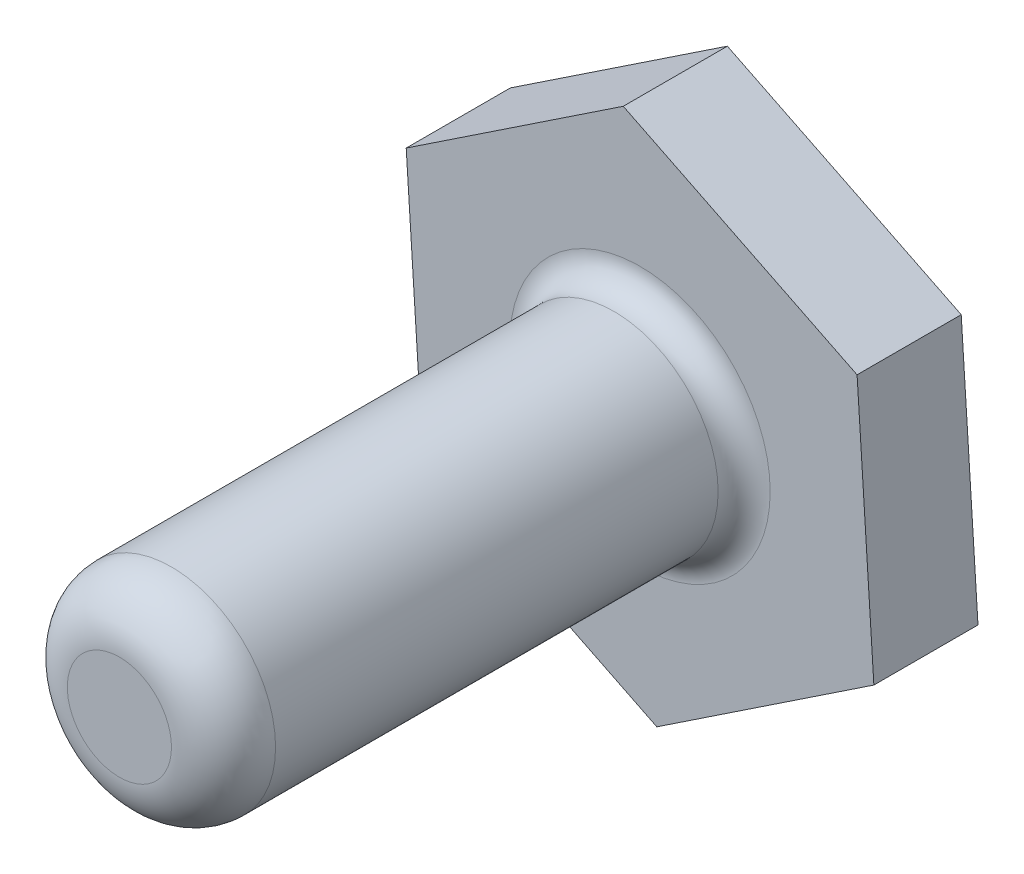
SolidWorks part; units mm, degrees
ref_plane "前视基准面" through (0, 0, 0) normal (0, 0, 1) x (1, 0, 0)
ref_plane "上视基准面" through (0, 0, 0) normal (0, 1, 0) x (1, 0, 0)
ref_plane "右视基准面" through (0, 0, 0) normal (1, 0, 0) x (0, 0, -1)
sketch "草图1" plane through (0, 0, 0) normal (0, 0, 1) x (1, 0, 0)
  line L1 (-8.3379, -5.5584) -> (0.6448, -10)
  line L2 (0.6448, -10) -> (8.9827, -4.4416)
  line L3 (8.9827, -4.4416) -> (8.3379, 5.5584)
  line L4 (8.3379, 5.5584) -> (-0.6448, 10)
  line L5 (-0.6448, 10) -> (-8.9827, 4.4416)
  line L6 (-8.9827, 4.4416) -> (-8.3379, -5.5584)
  circle A0 centre (0, 0) radius 8.6782 construction
  dimension "D1" = 10
extrude "凸台-拉伸3" add sketch "草图1" along normal blind 4 contours L6 L1 L2 L3 L4 L5
sketch "草图3" plane through (0, 0, 4) normal (0, 0, 1) x (1, 0, 0)
  circle A0 centre (0, 0) radius 4
  dimension "D1" = 8
extrude "凸台-拉伸4" add sketch "草图3" along normal blind 20
fillet "圆角1" radius 1 1 edges at (4, 0, 4)
fillet "圆角2" radius 2 1 edges at (4, 0, 24)
